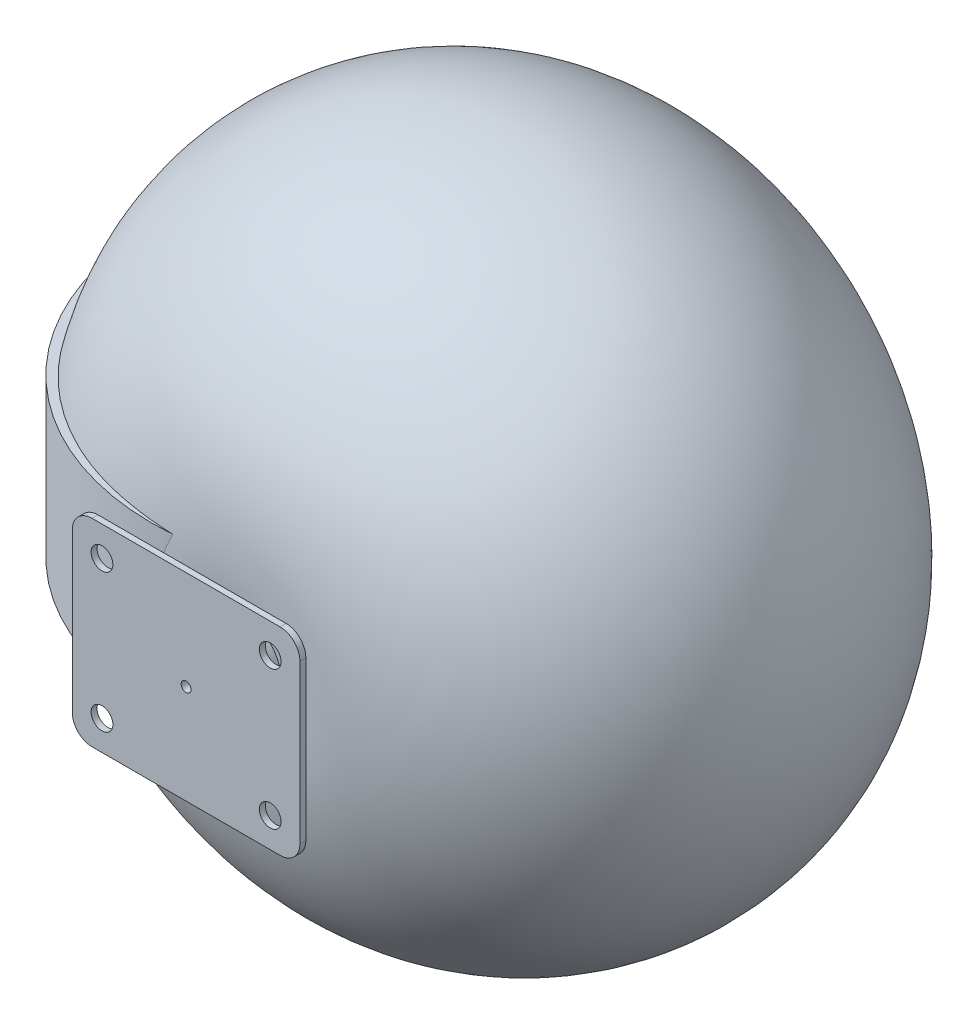
SolidWorks part; units mm, degrees
ref_plane "Ebene vorne" through (0, 0, 0) normal (0, 0, 1) x (1, 0, 0)
ref_plane "Ebene oben" through (0, 0, 0) normal (0, 1, 0) x (1, 0, 0)
ref_plane "Ebene rechts" through (0, 0, 0) normal (1, 0, 0) x (0, 0, -1)
sketch "Skizze1" plane through (0, 0, 0) normal (0, 0, 1) x (1, 0, 0)
  line L1 (57.5, -50) -> (-57.5, -50)
  line L2 (57.5, -50) -> (57.5, 50)
  line L3 (57.5, 50) -> (-57.5, 50)
  line L4 (-57.5, -50) -> (-57.5, 50)
  line L5 (57.5, -50) -> (-57.5, 50) construction
  line L6 (57.5, 50) -> (-57.5, -50) construction
  point P0 (0, 0)
  dimension "D1" = 100
  dimension "D2" = 115
extrude "Aufsatz-Linear austragen1" add sketch "Skizze1" along normal blind 3
sketch "Skizze2" plane through (0, 0, 3) normal (0, 0, 1) x (1, 0, 0)
  line L1 (42.5, -35) -> (-42.5, -35) construction
  line L2 (42.5, -35) -> (42.5, 35) construction
  line L3 (42.5, 35) -> (-42.5, 35) construction
  line L4 (-42.5, -35) -> (-42.5, 35) construction
  line L5 (42.5, -35) -> (-42.5, 35) construction
  line L6 (42.5, 35) -> (-42.5, -35) construction
  circle A0 centre (-42.5, 35) radius 5.5
  circle A1 centre (42.5, 35) radius 5.5
  circle A2 centre (42.5, -35) radius 5.5
  circle A3 centre (-42.5, -35) radius 5.5
  point P0 (0, 0)
  dimension "D1" = 11
  dimension "D2" = 85
  dimension "D3" = 70
extrude "Schnitt-Linear austragen1" cut sketch "Skizze2" against normal blind 5
fillet "Verrundung1" radius 10 4 edges at (-57.5, -50, 1.5) (57.5, -50, 1.5) (57.5, 50, 1.5) (-57.5, 50, 1.5)
sketch "Skizze3" plane through (0, 0, 0) normal (0, 0, -1) x (-1, 0, 0)
  circle A0 centre (0, 0) radius 2.5
  dimension "D1" = 5
extrude "Schnitt-Linear austragen2" cut sketch "Skizze3" against normal blind 10
sketch "Skizze4" plane through (0, 0, 0) normal (0, 0, -1) x (-1, 0, 0)
  circle A0 centre (0, 0) radius 25
  circle A1 centre (0, 0) radius 2.5 construction
  circle A2 centre (0, 0) radius 2.5
  dimension "D1" = 50
extrude "Aufsatz-Linear austragen2" add sketch "Skizze4" along normal blind 150
sketch "Skizze5" plane through (0, 0, 0) normal (0, 1, 0) x (1, 0, 0)
  line L0 (0, 0) -> (0, 150) construction
  line L1 (25, 150) -> (-25, 150) construction
  line L2 (0, 150) -> (-40, 150) construction
  circle A0 centre (-40, 150) radius 130
  dimension "D2" = 260
  dimension "D1" = 40
extrude "Aufsatz-Linear austragen3" add sketch "Skizze5" along normal mid plane 80
sketch "Skizze6" plane through (0, 0, 0) normal (0, 1, 0) x (1, 0, 0)
  line L0 (0, 0) -> (0, 273.6932) construction
  line L1 (0, 273.6932) -> (0, 26.3068)
  circle A0 centre (-40, 150) radius 130 construction
  arc A1 (0, 273.6932) -> (0, 26.3068) centre (-40, 150) ccw
  point P6 (0, 273.6932)
revolve "Rotation3" add sketch "Skizze6" angle 360 about L0
sketch "Skizze7" plane through (0, -40, 0) normal (0, -1, 0) x (1, 0, 0)
  circle A0 centre (-40, -150) radius 130
  arc A1 (-30, -20.3852) -> (-30, -279.6148) centre (-40, -150) ccw construction
extrude "Aufsatz-Linear austragen4" add sketch "Skizze7" against normal up to surface (80 mm away) up to face at (-2.7101, 40, -156.3863)
